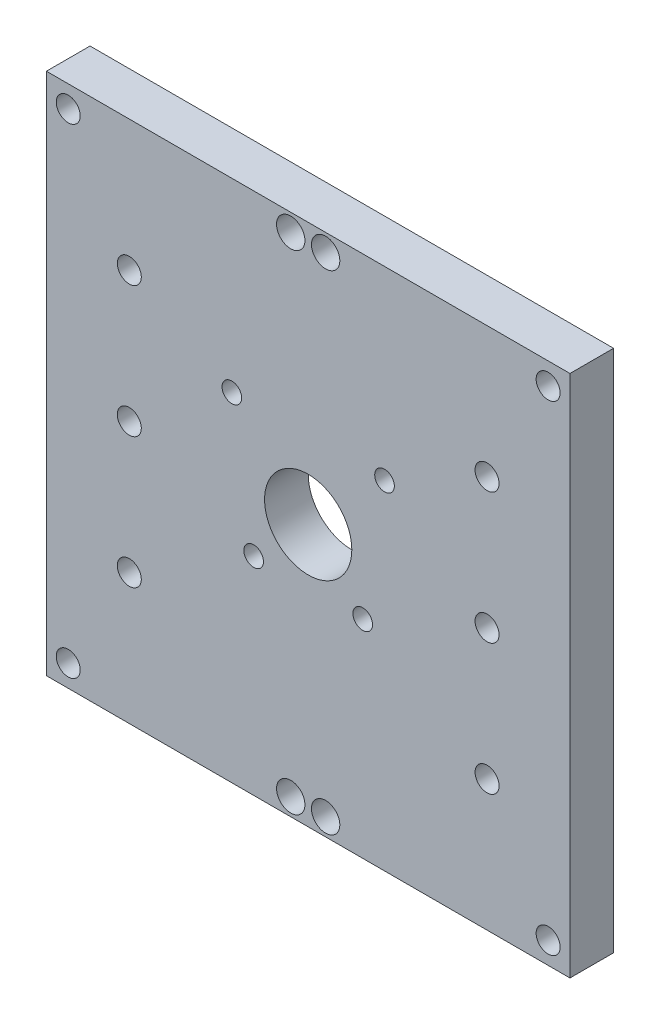
SolidWorks part; units mm, degrees
ref_plane "Front Plane" through (0, 0, 0) normal (0, 0, 1) x (1, 0, 0)
ref_plane "Top Plane" through (0, 0, 0) normal (0, 1, 0) x (1, 0, 0)
ref_plane "Right Plane" through (0, 0, 0) normal (1, 0, 0) x (0, 0, -1)
sketch "Sketch1" plane through (0, 0, 0) normal (0, 1, 0) x (1, 0, 0)
  line L1 (-60, -5) -> (60, -5)
  line L2 (-60, -5) -> (-60, 5)
  line L3 (-60, 5) -> (60, 5)
  line L4 (60, -5) -> (60, 5)
  line L5 (-60, -5) -> (60, 5) construction
  line L6 (-60, 5) -> (60, -5) construction
  point P0 (0, 0)
  dimension "D1" = 120
  dimension "D2" = 10
extrude "Boss-Extrude1" add sketch "Sketch1" along normal blind 120
sketch "Sketch2" plane through (0, 0, 5) normal (0, 0, 1) x (1, 0, 0)
  line L0 (60, 120) -> (-60, 120) construction
  line L1 (60, 0) -> (-60, 0) construction
  line L2 (-15, 50) -> (-15, 75)
  line L4 (-20, 75) -> (-20, 45)
  line L5 (-20, 45) -> (-15, 45)
  line L6 (60, 120) -> (60, 0) construction
  line L11 (15, 50) -> (15, 75)
  line L13 (20, 75) -> (20, 45)
  line L14 (20, 45) -> (15, 45)
  line L16 (-15, 50) -> (-10, 50)
  line L17 (-10, 50) -> (-10, 45)
  line L18 (-10, 45) -> (-15, 45)
  line L19 (15, 45) -> (10, 45)
  line L20 (10, 45) -> (10, 50)
  line L21 (10, 50) -> (15, 50)
  line L22 (15, 75) -> (15, 80)
  line L23 (15, 80) -> (20, 80)
  line L24 (20, 80) -> (20, 75)
  line L25 (-15, 75) -> (-15, 80)
  line L26 (-15, 80) -> (-20, 80)
  line L27 (-20, 80) -> (-20, 75)
  line L28 (-60, 120) -> (60, 120) construction
  line L29 (-60, 120) -> (-60, 0) construction
  line L30 (-60, 0) -> (60, 0) construction
  circle A0 centre (0, 60) radius 10
  circle A1 centre (-41, 60) radius 2.75
  circle A2 centre (-41, 30) radius 2.75
  circle A3 centre (-41, 90) radius 2.75
  circle A4 centre (41, 60) radius 2.75
  circle A5 centre (41, 30) radius 2.75
  circle A6 centre (41, 90) radius 2.75
  circle A7 centre (-4, 116) radius 3.25
  circle A8 centre (4, 116) radius 3.25
  circle A9 centre (-4, 4) radius 3.25
  circle A10 centre (4, 4) radius 3.25
  circle A11 centre (-12.5, 47.5) radius 2.25
  circle A12 centre (-17.5, 77.5) radius 2.25
  circle A13 centre (17.5, 77.5) radius 2.25
  circle A14 centre (12.5, 47.5) radius 2.25
  circle A15 centre (55, 115) radius 2.75
  circle A16 centre (-55, 115) radius 2.75
  circle A17 centre (55, 5) radius 2.75
  circle A18 centre (-55, 5) radius 2.75
  point P0 (0, 0)
  point P1 (0, 60)
  dimension "D3" = 41
  dimension "D4" = 30
  dimension "D9" = 4
  dimension "D14" = 4
  dimension "D15" = 8
  dimension "D16" = 20
  dimension "D17" = 2.5
  dimension "D28" = 5
  dimension "D30" = 5
  dimension "D32" = 5
  dimension "D1" = 60
  dimension "D2" = 60
  dimension "D5" = 30
  dimension "D6" = 41
  dimension "D7" = 30
  dimension "D8" = 30
  dimension "D10" = 4
  dimension "D11" = 4
  dimension "D12" = 0
  dimension "D13" = 0
  dimension "D18" = 15
  dimension "D19" = 60
  dimension "D20" = 15
  dimension "D21" = 2.5
  dimension "D22" = 2.5
  dimension "D23" = 2.5
  dimension "D24" = 2.5
  dimension "D25" = 2.5
  dimension "D26" = 2.5
  dimension "D27" = 2.5
  dimension "D29" = 5
  dimension "D31" = 5
extrude "Cut-Extrude1" cut sketch "Sketch2" against normal blind 10 contours A12 | A11 | A14 | A13 | A17 | A15 | A0 | A3 | A1 | A2 | A5 | A4 | A7 | A8 | A6 | A9 | A10 | A18 | A16
